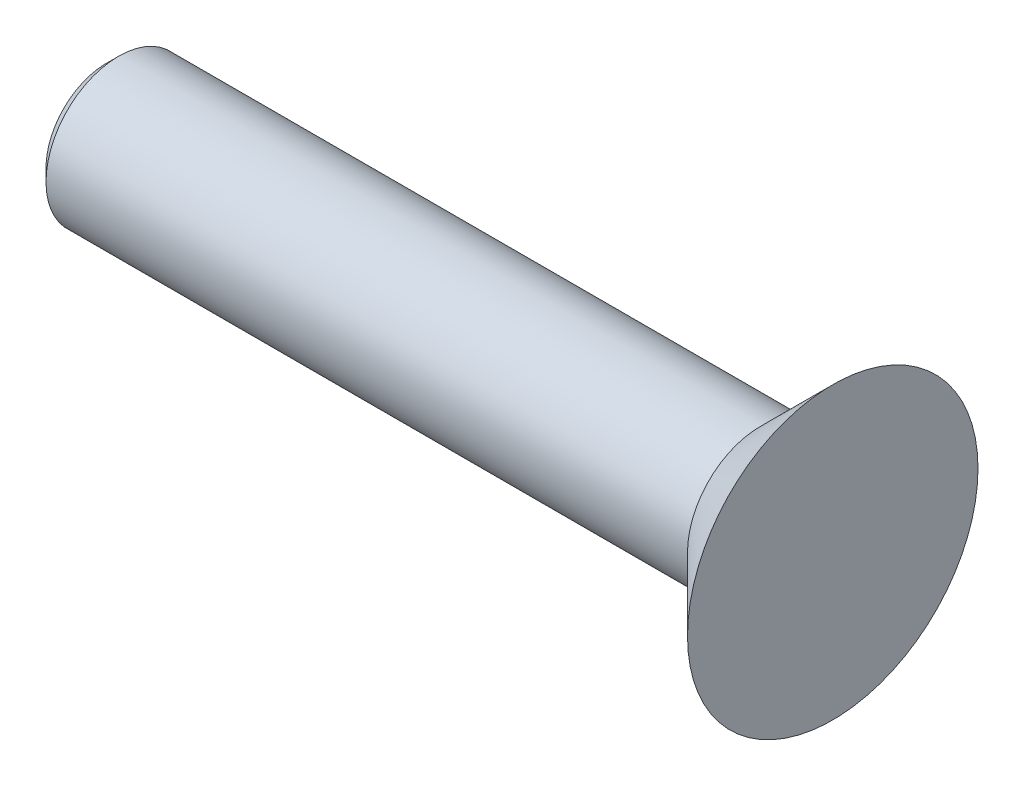
SolidWorks part; units mm, degrees
ref_plane "Plan de face" through (0, 0, 0) normal (0, 0, 1) x (1, 0, 0)
ref_plane "Plan de dessus" through (0, 0, 0) normal (0, 1, 0) x (1, 0, 0)
ref_plane "Plan de droite" through (0, 0, 0) normal (1, 0, 0) x (0, 0, -1)
sketch "Esquisse1" plane through (0, 0, 0) normal (0, 0, 1) x (1, 0, 0)
  line L0 (0, 0) -> (-15, 0)
  line L1 (-15, 0) -> (-15, 1.5)
  line L2 (-15, 1.5) -> (-1.5, 1.5)
  line L3 (-1.5, 1.5) -> (0, 3)
  line L4 (0, 3) -> (0, 0)
  line L5 (0, 0) -> (21.1509, 0) construction
  dimension "D1" = 45
  dimension "D2" = 1.5
  dimension "D3" = 3
  dimension "D4" = 15
revolve "Révolution1" add sketch "Esquisse1" angle 360 about L5
cosmetic thread "Représentation de filetage1" parameters "D2"=2.5
chamfer "Chanfrein1" distance 0.25 angle 45 1 edges at (-15, 0, 1.5)
